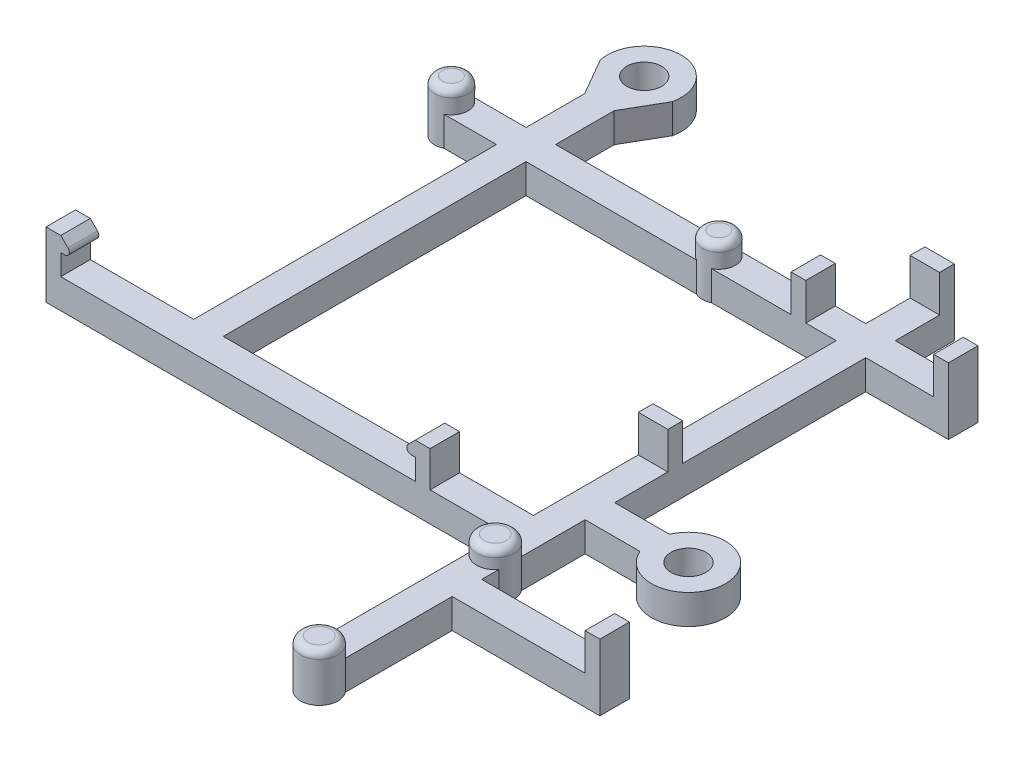
SolidWorks part; units mm, degrees
ref_plane "Front Plane" through (0, 0, 0) normal (0, 0, 1) x (1, 0, 0)
ref_plane "Top Plane" through (0, 0, 0) normal (0, 1, 0) x (1, 0, 0)
ref_plane "Right Plane" through (0, 0, 0) normal (1, 0, 0) x (0, 0, -1)
sketch "Sketch1" plane through (0, 0, 0) normal (0, 1, 0) x (1, 0, 0)
  line L58 (-10.16, -22.86) -> (-10.16, -5.715)
  line L65 (-7.62, -1.27) -> (-2.9099, -1.27)
  line L83 (-10.16, 30.48) -> (-7.62, 30.48)
  line L90 (-7.62, 30.48) -> (-7.62, 25.4)
  line L92 (-10.16, 25.4) -> (-10.16, 30.48)
  line L93 (-49.53, 25.4) -> (-39.37, 25.4)
  line L94 (-49.53, 25.4) -> (-49.53, 22.86)
  line L95 (-49.53, 22.86) -> (-39.37, 22.86)
  line L102 (-0.508, 25.4) -> (-0.508, 22.86)
  line L114 (-7.62, 22.86) -> (-7.62, 1.27)
  line L115 (-7.62, 25.4) -> (-0.508, 25.4)
  line L116 (-7.62, 22.86) -> (-0.508, 22.86)
  line L117 (-7.62, 1.27) -> (-2.9099, 1.27)
  line L118 (-41.2031, 33.6181) -> (-39.37, 30.4431)
  line L119 (-39.37, 30.4431) -> (-39.37, 25.4)
  line L120 (-39.37, -3.175) -> (-36.83, -3.175) construction
  line L122 (-38.1, 34.29) -> (-38.1, 0) construction
  line L125 (-36.83, -3.175) -> (-36.83, 22.86)
  line L126 (-36.83, 30.4431) -> (-34.9969, 33.6181)
  line L127 (-39.37, 30.4431) -> (-36.83, 30.4431) construction
  line L128 (-39.37, -3.175) -> (-49.53, -3.175)
  line L129 (-49.53, -3.175) -> (-49.53, -5.715)
  line L130 (-49.53, -5.715) -> (-10.16, -5.715)
  line L132 (-10.16, -3.175) -> (-36.83, -3.175)
  line L133 (-36.83, 25.4) -> (-10.16, 25.4)
  line L134 (-36.83, 25.4) -> (-36.83, 30.4431)
  line L135 (-36.83, 22.86) -> (-10.16, 22.86)
  line L136 (-39.37, 22.86) -> (-39.37, -3.175)
  line L137 (-7.62, -10.16) -> (5.08, -10.16)
  line L138 (-41.2031, 33.6181) -> (-34.9969, 33.6181) construction
  line L141 (-1.5, 0) -> (0, 0) construction
  line L147 (-10.16, -22.86) -> (-7.62, -22.86)
  line L148 (-7.62, -1.27) -> (-7.62, -10.16)
  line L152 (5.08, -10.16) -> (5.08, -12.7)
  line L153 (-7.62, -12.7) -> (5.08, -12.7)
  line L155 (-7.62, -12.7) -> (-7.62, -22.86)
  line L156 (-10.16, -3.175) -> (-10.16, 22.86)
  circle A7 centre (-38.1, 34.29) radius 1.5
  arc A9 (-34.9969, 33.6181) -> (-41.2031, 33.6181) centre (-38.1, 34.29) ccw
  circle A14 centre (0, 0) radius 1.5
  arc A17 (-2.9099, -1.27) -> (-2.9099, 1.27) centre (0, 0) ccw
  point P1 (-5.265, 1.27)
  point P27 (-38.1, -3.175)
  point P39 (-38.1, 34.29)
  dimension "D4" = 3
  dimension "D11" = 7.112
  dimension "D20" = 21.59
  dimension "D9" = 34.29
  dimension "D3" = 3
  dimension "D10" = 3.175
  dimension "D7" = 3.175
  dimension "D5" = 2.54
  dimension "D6" = 3.175
  dimension "D8" = 38.1
  dimension "D12" = 2.54
  dimension "D13" = 2.54
  dimension "D14" = 30
  dimension "D15" = 2.54
  dimension "D16" = 2.54
  dimension "D17" = 5.08
  dimension "D18" = 8.89
  dimension "D19" = 26.67
  dimension "D21" = 28.575
  dimension "D22" = 38.1
  dimension "D23" = 11.43
  dimension "D24" = 2.54
  dimension "D25" = 2.54
  dimension "D26" = 10.16
  dimension "D27" = 12.7
extrude "Boss-Extrude1" add sketch "Sketch1" along normal blind 2.54
sketch "Sketch3" plane through (0, 0, -22.86) normal (0, 0, 1) x (1, 0, 0)
  line L0 (-49.53, 2.54) -> (-49.53, 5.61)
  line L1 (-49.53, 5.61) -> (-48.26, 5.61)
  line L2 (-48.26, 5.61) -> (-46.99, 4.34)
  line L3 (-46.99, 4.34) -> (-48.26, 4.34)
  line L4 (-48.26, 4.34) -> (-48.26, 2.54)
  line L5 (-49.53, 2.54) -> (-10.16, 2.54) construction
  line L6 (-49.53, 2.54) -> (-48.26, 2.54)
  line L7 (-49.53, 2.54) -> (-0.508, 2.54) construction
  line L8 (-1.778, 5.715) -> (-1.778, 2.54)
  line L9 (-25.019, 2.54) -> (-25.019, 7.4356) construction
  line L10 (-0.508, 2.54) -> (-1.778, 2.54)
  line L14 (-0.508, 5.715) -> (-1.778, 5.715)
  line L15 (-0.508, 2.54) -> (-0.508, 5.715)
  line L16 (0, 0) -> (0, 5.4399) construction
  line L23 (-16.51, 2.54) -> (-17.78, 2.54)
  line L24 (-17.78, 4.34) -> (-17.78, 2.54)
  line L25 (-19.05, 4.34) -> (-17.78, 4.34)
  line L26 (-17.78, 5.61) -> (-19.05, 4.34)
  line L27 (-16.51, 5.61) -> (-17.78, 5.61)
  line L28 (-16.51, 2.54) -> (-16.51, 5.61)
  line L29 (-14.0462, 2.54) -> (-14.0462, 5.715)
  line L30 (-14.0462, 5.715) -> (-12.7762, 5.715)
  line L33 (-12.7762, 5.715) -> (-12.7762, 2.54)
  line L34 (-14.0462, 2.54) -> (-12.7762, 2.54)
  arc A0 (-47.625, 4.975) -> (-47.888, 4.34) centre (-47.888, 4.712) cw construction
  dimension "D1" = 1.8
  dimension "D2" = 1.27
  dimension "D3" = 1.27
  dimension "D4" = 45
  dimension "D5" = 1.27
  dimension "D6" = 45
  dimension "D7" = 1.8
  dimension "D8" = 10.9982
  dimension "D9" = 1.27
  dimension "D10" = 3.175
  dimension "D11" = 3.175
  dimension "D13" = 33.02
extrude "Boss-Extrude3" add sketch "Sketch3" against normal blind 2.54
sketch "Sketch4" plane through (0, 0, 5.715) normal (0, 0, 1) x (1, 0, 0)
  line L2 (-17.78, 2.54) -> (-16.51, 2.54)
  line L3 (-49.53, 2.54) -> (-48.26, 2.54)
  line L10 (-49.53, 0) -> (-39.37, 0)
  line L12 (-39.37, 0) -> (-39.37, 2.54)
  line L13 (-39.37, 2.54) -> (-48.26, 2.54)
  line L14 (-48.26, 2.54) -> (-48.26, 4.34)
  line L24 (-48.26, 4.34) -> (-46.99, 4.34)
  line L32 (-46.99, 4.34) -> (-48.26, 5.61)
  line L34 (-48.26, 5.61) -> (-49.53, 5.61)
  line L35 (-49.53, 5.61) -> (-49.53, 0)
  line L46 (-48.26, 2.54) -> (-48.26, 4.34)
  line L47 (-48.26, 4.34) -> (-46.99, 4.34)
  line L64 (-46.99, 4.34) -> (-48.26, 5.61)
  line L65 (-48.26, 5.61) -> (-49.53, 5.61)
  line L66 (-49.53, 5.61) -> (-49.53, 2.54)
  line L76 (-36.83, 0) -> (-10.16, 0)
  line L78 (-10.16, 2.54) -> (-12.7762, 2.54)
  line L79 (-12.7762, 2.54) -> (-12.7762, 5.715)
  line L82 (-12.7762, 5.715) -> (-14.0462, 5.715)
  line L83 (-14.0462, 5.715) -> (-14.0462, 2.54)
  line L84 (-14.0462, 2.54) -> (-16.51, 2.54)
  line L85 (-16.51, 2.54) -> (-16.51, 5.61)
  line L86 (-16.51, 5.61) -> (-17.78, 5.61)
  line L87 (-17.78, 5.61) -> (-19.05, 4.34)
  line L88 (-19.05, 4.34) -> (-17.78, 4.34)
  line L89 (-17.78, 4.34) -> (-17.78, 2.54)
  line L90 (-17.78, 2.54) -> (-36.83, 2.54)
  line L91 (-36.83, 2.54) -> (-36.83, 0)
  line L101 (-16.51, 2.54) -> (-16.51, 5.61)
  line L102 (-16.51, 5.61) -> (-17.78, 5.61)
  line L103 (-17.78, 5.61) -> (-19.05, 4.34)
  line L104 (-19.05, 4.34) -> (-17.78, 4.34)
  line L105 (-17.78, 4.34) -> (-17.78, 2.54)
  line L110 (-10.16, 0) -> (-10.16, 2.54)
  dimension "D1" = 0
  dimension "D2" = 0
extrude "Boss-Extrude4" add sketch "Sketch4" against normal blind 2.54
sketch "Sketch5" plane through (-7.62, 0, 0) normal (1, 0, 0) x (0, 0, -1)
  line L0 (5.842, 2.54) -> (5.842, 5.715)
  line L1 (5.842, 5.715) -> (7.112, 5.715)
  line L5 (5.842, 2.54) -> (7.112, 2.54)
  line L6 (1.27, 2.54) -> (22.86, 2.54) construction
  line L7 (30.48, 2.54) -> (29.21, 2.54)
  line L8 (25.4, 2.54) -> (30.48, 2.54) construction
  line L10 (7.112, 2.54) -> (29.21, 2.54) construction
  line L11 (18.161, 2.54) -> (18.161, 5.1337) construction
  line L16 (30.48, 2.54) -> (30.48, 5.715)
  line L17 (30.48, 5.715) -> (29.21, 5.715)
  line L24 (7.112, 5.715) -> (7.112, 2.54)
  line L27 (29.21, 5.715) -> (29.21, 2.54)
  dimension "D1" = 3.175
  dimension "D2" = 1.27
  dimension "D5" = 22.098
extrude "Boss-Extrude5" add sketch "Sketch5" against normal blind 2.54
sketch "Sketch7" plane through (0, 0, 12.7) normal (0, 0, 1) x (1, 0, 0)
  line L8 (-3.5179, 2.54) -> (5.08, 2.54) construction
  line L9 (-3.5179, 2.54) -> (-3.5179, 4.6682) construction
  line L10 (3.81, 2.54) -> (5.08, 2.54)
  line L11 (3.81, 5.715) -> (3.81, 2.54)
  line L14 (5.08, 5.715) -> (3.81, 5.715)
  line L15 (5.08, 2.54) -> (5.08, 5.715)
  line L16 (-36.83, 0) -> (-10.16, 0)
  line L17 (-10.16, 0) -> (-10.16, 2.54)
  line L18 (-10.16, 2.54) -> (-12.7762, 2.54)
  line L19 (-12.7762, 2.54) -> (-12.7762, 5.715)
  line L22 (-12.7762, 5.715) -> (-14.0462, 5.715)
  line L23 (-14.0462, 5.715) -> (-14.0462, 2.54)
  line L24 (-14.0462, 2.54) -> (-16.51, 2.54)
  line L25 (-16.51, 2.54) -> (-16.51, 5.61)
  line L26 (-16.51, 5.61) -> (-17.78, 5.61)
  line L27 (-17.78, 5.61) -> (-19.05, 4.34)
  line L28 (-19.05, 4.34) -> (-17.78, 4.34)
  line L29 (-17.78, 4.34) -> (-17.78, 2.54)
  line L30 (-17.78, 2.54) -> (-36.83, 2.54)
  line L31 (-36.83, 2.54) -> (-36.83, 0)
  line L47 (-36.83, 2.54) -> (-36.83, 0)
  dimension "D2" = 1.27
  dimension "D3" = 3.175
  dimension "D1" = 0
extrude "Boss-Extrude6" add sketch "Sketch7" against normal blind 2.54
fillet "Fillet1" radius 0.381 4 edges at (-19.05, 4.34, -24.13) (-46.99, 4.34, -24.13) (-19.05, 4.34, 4.445) (-46.99, 4.34, 4.445)
sketch "Sketch11" plane through (0, 0, -22.86) normal (0, 0, 1) x (1, 0, 0)
  line L0 (-49.53, 0) -> (-10.16, 0) construction
  line L1 (-49.53, 5.61) -> (-45.0244, 5.61)
  line L2 (-49.53, 5.61) -> (-49.53, 0)
  line L3 (-49.53, 0) -> (-45.0244, 0)
  line L4 (-45.0244, 5.61) -> (-45.0244, 0)
  line L5 (-48.26, 2.54) -> (-17.78, 2.54) construction
  line L6 (-16.51, 5.61) -> (-18.9109, 5.61)
  line L7 (-16.51, 5.61) -> (-16.51, 2.54)
  line L8 (-16.51, 2.54) -> (-18.9109, 2.54)
  line L9 (-18.9109, 5.61) -> (-18.9109, 2.54)
extrude "Cut-Extrude2" cut sketch "Sketch11" against normal up to next
sketch "Sketch8" plane through (0, 2.54, 0) normal (0, 1, 0) x (1, 0, 0)
  line L0 (-21.52, 24.13) -> (-44.52, 24.13) construction
  line L1 (-14.0462, 25.4) -> (-36.83, 25.4) construction
  line L2 (-14.0462, 25.4) -> (-36.83, 25.4) construction
  line L3 (-14.0462, 22.86) -> (-36.83, 22.86) construction
  line L4 (-33.02, 24.13) -> (-33.02, 22.86) construction
  line L5 (-48.26, 22.86) -> (-17.78, 22.86) construction
  line L6 (-33.02, 24.13) -> (-33.02, 25.4) construction
  line L7 (-48.26, -3.175) -> (-48.26, -5.715) construction
  line L8 (-17.78, -3.175) -> (-17.78, -5.715) construction
  circle A0 centre (-44.52, 24.13) radius 1.4224
  circle A1 centre (-21.52, 24.13) radius 1.4224
  point P7 (-33.02, 24.13)
  dimension "D2" = 2.8448
  dimension "D1" = 23
extrude "Boss-Extrude7" add sketch "Sketch8" along normal blind 1.905 and the other way up to surface (2.54 mm away) other way up to face at (0, 0, 1.5)
sketch "Sketch10" plane through (0, 2.54, 0) normal (0, 1, 0) x (1, 0, 0)
  line L0 (-8.89, -7.7216) -> (-8.89, -22.86) construction
  line L2 (-10.16, -15.2908) -> (-8.89, -15.2908) construction
  line L3 (-10.16, -22.86) -> (-7.62, -22.86) construction
  line L4 (-8.89, -15.2908) -> (-7.62, -15.2908) construction
  line L5 (-7.62, -22.86) -> (-7.62, -12.7) construction
  circle A0 centre (-8.89, -7.7216) radius 1.6002
  circle A1 centre (-8.89, -22.86) radius 1.6002
  point P10 (-8.89, -6.1214)
  point P11 (-8.89, -24.4602)
  dimension "D1" = 3.2004
  dimension "D2" = 18.3388
extrude "Boss-Extrude8" add sketch "Sketch10" along normal blind 1.524 and the other way up to surface (2.54 mm away) other way up to face at (-19.7329, 0, -11.8282)
fillet "Fillet2" radius 0.635 4 edges at (-21.52, 4.445, -22.7076) (-44.52, 4.445, -22.7076) (-8.89, 4.064, 24.4602) (-8.89, 4.064, 9.3218)
